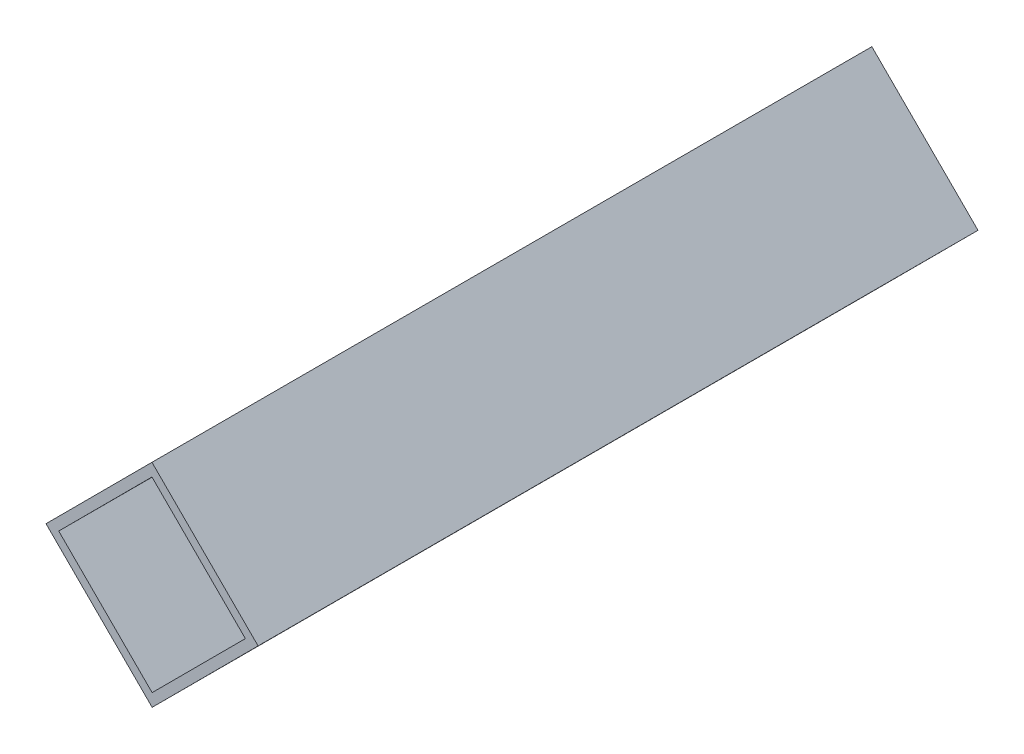
SolidWorks part; units mm, degrees
material "可鍛鑄鐵"
ref_plane "前基準面" through (0, 0, 0) normal (0, 0, 1) x (1, 0, 0)
ref_plane "上基準面" through (0, 0, 0) normal (0, 1, 0) x (1, 0, 0)
ref_plane "右基準面" through (0, 0, 0) normal (1, 0, 0) x (0, 0, -1)
sketch "草圖1" plane through (0, 0, 0) normal (0, 0, 1) x (1, 0, 0)
  line L0 (0, 0) -> (17.6938, -17.6615)
  line L1 (0, 0) -> (-17.6615, -17.6938)
  line L2 (17.6938, -17.6615) -> (0.0323, -35.3553)
  line L3 (-17.6615, -17.6938) -> (0.0323, -35.3553)
  line L4 (0.0019, -2.1213) -> (-15.5402, -17.6919)
  line L5 (0.0019, -2.1213) -> (15.5725, -17.6635)
  line L6 (-15.5402, -17.6919) -> (0.0303, -33.234)
  line L7 (15.5725, -17.6635) -> (0.0303, -33.234)
  point P0 (8.8469, -8.8308)
  dimension "D1" = 25
  dimension "D2" = 25
  dimension "D3" = 1.5
  dimension "D4" = 1.5
  dimension "D5" = 1.5
  dimension "D6" = 1.5
extrude "填料-伸長1" add sketch "草圖1" along normal blind 120
sketch "草圖2" plane through (0, 0, 0) normal (0.7065, 0.7078, 0) x (0.7078, -0.7065, 0)
  line L0 (25, -120) -> (0, -120) construction
  line L1 (25, -120) -> (25, 0) construction
  line L2 (25, 0) -> (0, 0) construction
  line L3 (0, -120) -> (0, 0) construction
  circle A0 centre (12.5, 52) radius 2.75
  circle A1 centre (12.5, 8) radius 2.75
  circle A2 centre (12.5, -128) radius 2.75
  circle A3 centre (12.5, -172) radius 2.75
  dimension "D1" = 5.5
  dimension "D2" = 5.5
  dimension "D4" = 128
  dimension "D5" = 12.5
  dimension "D6" = 12.5
  dimension "D7" = 5.5
  dimension "D8" = 5.5
  dimension "D9" = 44
  dimension "D10" = 128
  dimension "D11" = 12.5
  dimension "D3" = 44
